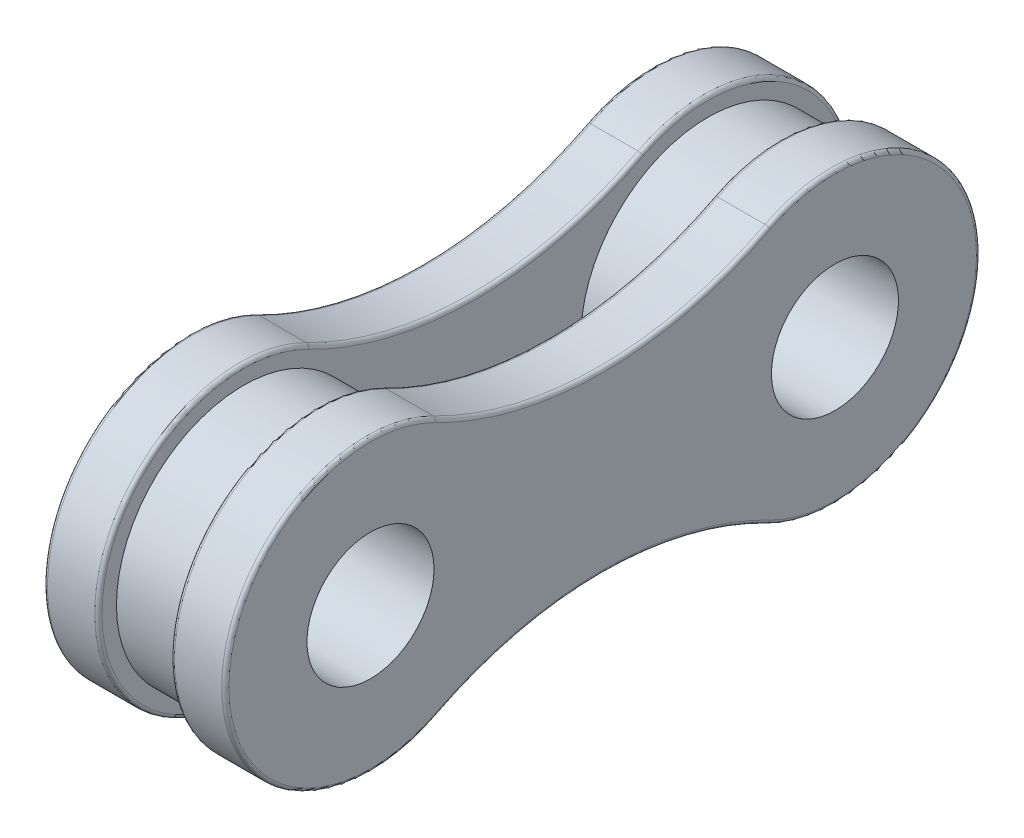
SolidWorks part; units mm, degrees
material "1060 Alloy"
ref_plane "Front Plane" through (0, 0, 0) normal (0, 0, 1) x (1, 0, 0)
ref_plane "Top Plane" through (0, 0, 0) normal (0, 1, 0) x (1, 0, 0)
ref_plane "Right Plane" through (0, 0, 0) normal (1, 0, 0) x (0, 0, -1)
sketch "Sketch1" plane through (0, 0, 0) normal (1, 0, 0) x (0, 0, -1)
  line L0 (6.3985, 0) -> (-6.3985, 0) construction
  line L1 (0, -12265.2787) -> (0, 12284.0066) construction
  arc A0 (-4.5704, 3.5578) -> (-4.5704, -3.5578) centre (-6.3985, 0) ccw
  circle A1 centre (-6.3985, 0) radius 1.75
  circle A2 centre (6.3985, 0) radius 1.75
  arc A3 (4.5704, 3.5578) -> (4.5704, -3.5578) centre (6.3985, 0) cw
  arc A4 (-4.5704, 3.5578) -> (4.5704, 3.5578) centre (0, 12.4523) ccw
  arc A5 (-4.5704, -3.5578) -> (4.5704, -3.5578) centre (0, -12.4523) cw
  dimension "D2" = 8
  dimension "D3" = 3.5
  dimension "D4" = 10
  dimension "D1" = 12.797
extrude "Boss-Extrude1" add sketch "Sketch1" along normal blind 1.5 from offset 1
sketch "Sketch2" plane through (0, 0, 0) normal (1, 0, 0) x (0, 0, -1)
  circle A0 centre (-6.3985, 0) radius 1.75 construction
  circle A1 centre (6.3985, 0) radius 1.75 construction
  circle A2 centre (-6.3985, 0) radius 1.75
  circle A3 centre (6.3985, 0) radius 1.75
  arc A4 (4.5704, -3.5578) -> (-4.5704, -3.5578) centre (0, -12.4523) ccw
  arc A5 (4.5704, -3.5578) -> (4.5704, 3.5578) centre (6.3985, 0) ccw
  arc A6 (-4.5704, 3.5578) -> (4.5704, 3.5578) centre (0, 12.4523) ccw
  arc A7 (-4.5704, 3.5578) -> (-4.5704, -3.5578) centre (-6.3985, 0) ccw
  arc A8 (4.5704, -3.5578) -> (-4.5704, -3.5578) centre (0, -12.4523) ccw
  arc A9 (4.5704, -3.5578) -> (4.5704, 3.5578) centre (6.3985, 0) ccw
  arc A10 (-4.5704, 3.5578) -> (4.5704, 3.5578) centre (0, 12.4523) ccw
  arc A11 (-4.5704, 3.5578) -> (-4.5704, -3.5578) centre (-6.3985, 0) ccw
  dimension "D1" = 0
extrude "Boss-Extrude2" add sketch "Sketch2" against normal blind 1.5 from offset 1 separate body offset against normal yes
sketch "Sketch3" plane through (0, 0, 0) normal (1, 0, 0) x (0, 0, -1)
  line L0 (0, -1146.9345) -> (0, 5479.7981) construction
  circle A0 centre (6.3985, 0) radius 1.75 construction
  circle A1 centre (-6.3985, 0) radius 1.75 construction
  circle A2 centre (6.3985, 0) radius 1.75
  circle A3 centre (-6.3985, 0) radius 1.75
  circle A4 centre (6.3985, 0) radius 3.5
  circle A5 centre (-6.3985, 0) radius 3.5
  dimension "D1" = 7
extrude "Boss-Extrude3" add sketch "Sketch3" along normal mid plane 2
fillet "Fillet1" radius 0.1 16 edges at (2.5, 0, 10.3985) (2.5, 2.4523, 0) (2.5, 0, -10.3985) (1, 0, 10.3985) (1, 2.4523, 0) (1, 0, -10.3985) (-1, 0, 10.3985) (-1, 2.4523, 0) (-1, 0, -10.3985) (-2.5, 0, 10.3985) (-2.5, 2.4523, 0) (-2.5, 0, -10.3985) (2.5, -2.4523, 0) (1, -2.4523, 0) (-1, -2.4523, 0) (-2.5, -2.4523, 0)
